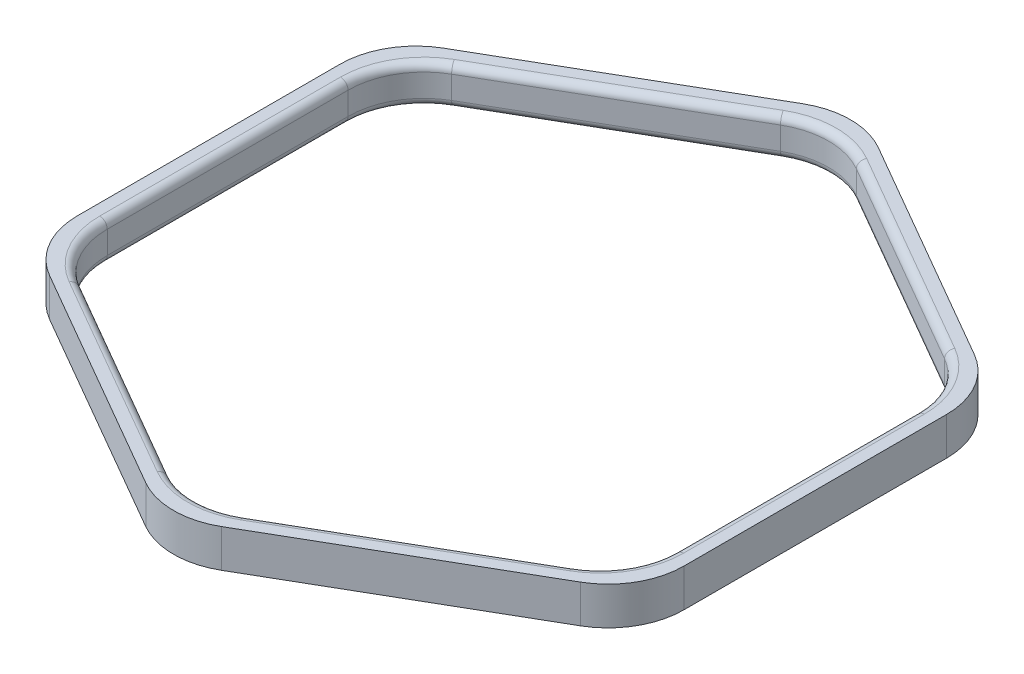
SolidWorks part; units mm, degrees
ref_plane "Piano frontale" through (0, 0, 0) normal (0, 0, 1) x (1, 0, 0)
ref_plane "Piano superiore" through (0, 0, 0) normal (0, 1, 0) x (1, 0, 0)
ref_plane "Piano destro" through (0, 0, 0) normal (1, 0, 0) x (0, 0, -1)
sketch "Schizzo2" plane through (0, 0, 0) normal (0, 1, 0) x (1, 0, 0)
  line L1 (40, 23.094) -> (0, 46.188)
  line L2 (0, 46.188) -> (-40, 23.094)
  line L3 (-40, 23.094) -> (-40, -23.094)
  line L4 (-40, -23.094) -> (0, -46.188)
  line L5 (0, -46.188) -> (40, -23.094)
  line L6 (40, -23.094) -> (40, 23.094)
  circle A0 centre (0, 0) radius 40 construction
  dimension "D1" = 80
extrude "Estrusione-Sottile1" add sketch "Schizzo2" along normal blind 5 thin thin type one direction reverse wall 2.5
fillet "Raccordo1" radius 10 12 edges at (37.5, 2.5, 21.6506) (0, 2.5, 43.3013) (37.5, 2.5, -21.6506) (0, 2.5, -43.3013) (-37.5, 2.5, -21.6506) (-37.5, 2.5, 21.6506) (40, 2.5, -23.094) (0, 2.5, -46.188) (-40, 2.5, -23.094) (-40, 2.5, 23.094) (0, 2.5, 46.188) (40, 2.5, 23.094)
fillet "Raccordo2" radius 1 24 edges at (-36.1603, 0, 20.8771) (-37.5, 0, 0) (-36.1603, 0, -20.8771) (-18.75, 0, -32.476) (0, 0, -41.7543) (18.75, 0, -32.476) (36.1603, 0, -20.8771) (37.5, 0, 0) (36.1603, 0, 20.8771) (18.75, 0, 32.476) (0, 0, 41.7543) (-36.1603, 5, 20.8771) (-37.5, 5, 0) (-36.1603, 5, -20.8771) (-18.75, 5, -32.476) (0, 5, -41.7543) (18.75, 5, -32.476) (36.1603, 5, -20.8771) (37.5, 5, 0) (36.1603, 5, 20.8771) (18.75, 5, 32.476) (0, 5, 41.7543) (-18.75, 0, 32.476) (-18.75, 5, 32.476)
